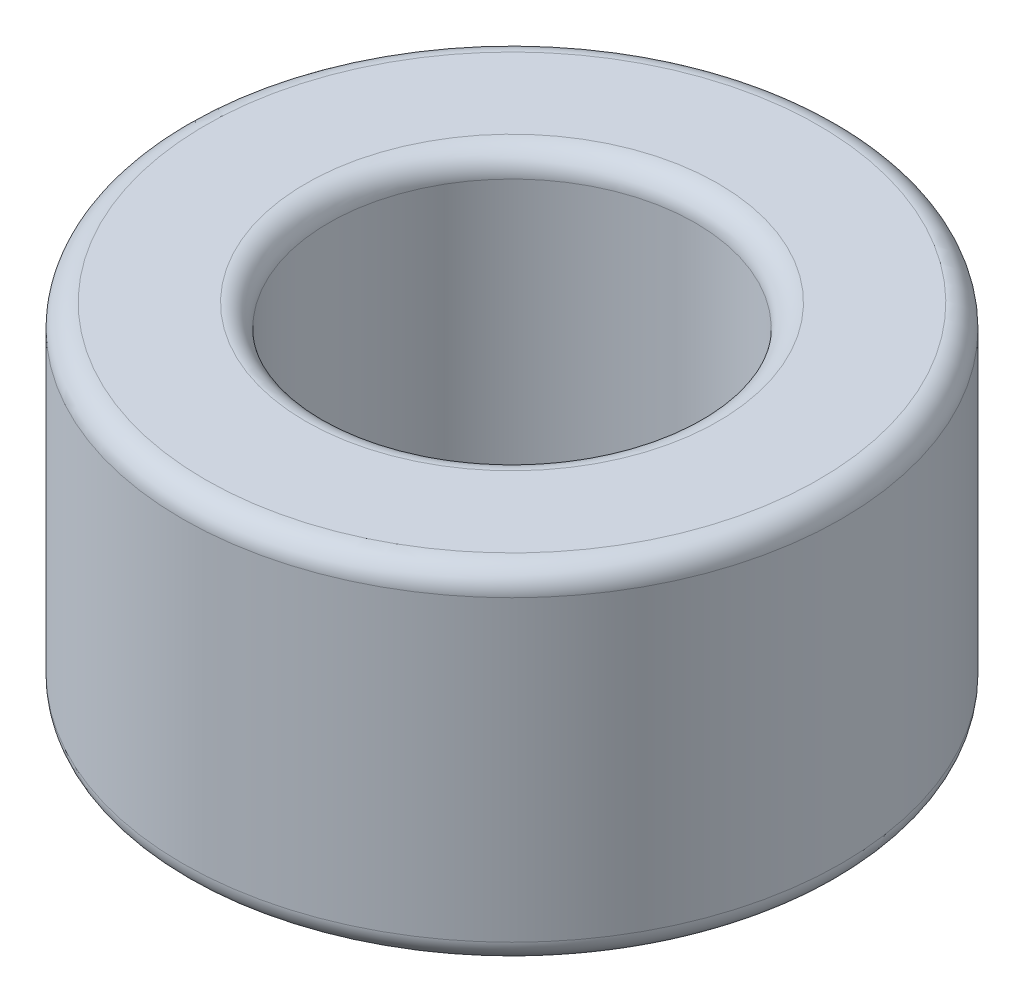
SolidWorks part; units mm, degrees
ref_plane "Front Plane" through (0, 0, 0) normal (0, 0, 1) x (1, 0, 0)
ref_plane "Top Plane" through (0, 0, 0) normal (0, 1, 0) x (1, 0, 0)
ref_plane "Right Plane" through (0, 0, 0) normal (1, 0, 0) x (0, 0, -1)
sketch "Sketch1" plane through (0, 0, 0) normal (0, 1, 0) x (1, 0, 0)
  circle A0 centre (0, 0) radius 2.875
  circle A1 centre (0, 0) radius 1.6
  dimension "D1" = 3.2
  dimension "D2" = 5.75
extrude "Boss-Extrude1" add sketch "Sketch1" along normal blind 3
fillet "Fillet1" radius 0.1984 4 edges at (0, 0, 1.6) (0, 0, 2.875) (0, 3, 1.6) (0, 3, 2.875)
